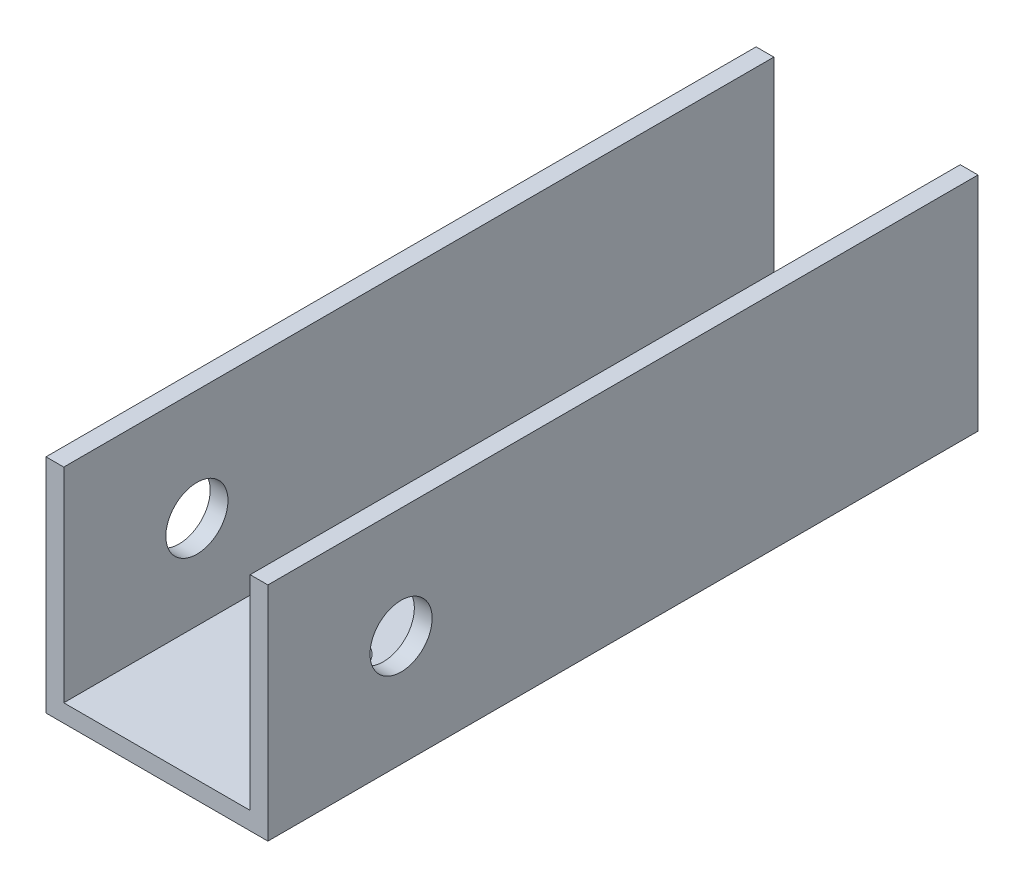
SolidWorks part; units mm, degrees
material "1060 Alloy"
ref_plane "Front" through (0, 0, 0) normal (0, 0, 1) x (1, 0, 0)
ref_plane "Top" through (0, 0, 0) normal (0, 1, 0) x (1, 0, 0)
ref_plane "Right" through (0, 0, 0) normal (1, 0, 0) x (0, 0, -1)
sketch "Sketch2" plane through (0, 0, 0) normal (0, 0, 1) x (1, 0, 0)
  line L0 (23, 25) -> (25, 25)
  line L1 (0, 0) -> (25, 0)
  line L2 (0, 0) -> (0, 25)
  line L3 (0, 25) -> (2, 25)
  line L4 (25, 0) -> (25, 25)
  line L6 (2, 25) -> (2, 2)
  line L7 (2, 2) -> (23, 2)
  line L8 (23, 25) -> (23, 2)
  dimension "D1" = 25
  dimension "D2" = 25
  dimension "D3" = 2
  dimension "D4" = 2
  dimension "D5" = 2
extrude "Boss-Extrude1" add sketch "Sketch2" along normal blind 80
sketch "Sketch3" plane through (25, 0, 0) normal (1, 0, 0) x (0, 0, -1)
  line L0 (-80, 0) -> (-80, 25) construction
  line L1 (-80, 25) -> (0, 25) construction
  circle A0 centre (-65, 12.5) radius 3.5
  dimension "D3" = 7
  dimension "D1" = 15
  dimension "D2" = 12.5
extrude "Cut-Extrude1" cut sketch "Sketch3" against normal up to surface (25 mm away) up to face at (0, 12.5, 40)
sketch "Sketch4" plane through (0, 0, 0) normal (0, -1, 0) x (1, 0, 0)
  line L0 (25, 40) -> (-49975, 40) construction
  line L1 (25, 80) -> (25, 0) construction
  line L2 (0, 80) -> (0, 0) construction
  line L3 (0, 80) -> (25, 80) construction
  circle A0 centre (12.5, 60) radius 3
  circle A1 centre (12.5, 20) radius 3
  point P4 (25, 40)
  point P7 (0, 40)
  dimension "D1" = 6
  dimension "D2" = 12.5
  dimension "D3" = 20
extrude "Cut-Extrude2" cut sketch "Sketch4" against normal up to next
